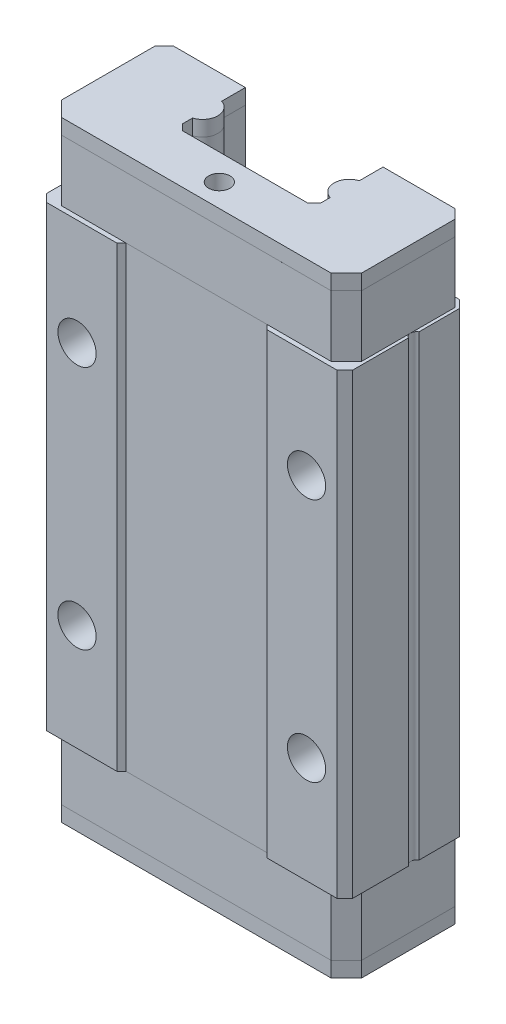
SolidWorks part; units mm, degrees
material "1.4301 (X5CrNi18-10)"
ref_plane "Horní rovina" through (0, 0, 0) normal (0, 0, 1) x (1, 0, 0)
ref_plane "Přední rovina" through (0, 0, 0) normal (0, 1, 0) x (1, 0, 0)
ref_plane "Pravá rovina" through (0, 0, 0) normal (1, 0, 0) x (0, 0, -1)
sketch "Skica1" plane through (0, 0, 0) normal (0, 0, 1) x (1, 0, 0)
  line L1 (-10, 14.95) -> (10, 14.95)
  line L2 (-10, 14.95) -> (-10, -14.95)
  line L3 (-10, -14.95) -> (10, -14.95)
  line L4 (10, 14.95) -> (10, -14.95)
  line L5 (-10, 14.95) -> (10, -14.95) construction
  line L6 (-10, -14.95) -> (10, 14.95) construction
  point P0 (0, 0)
  dimension "D1" = 20
  dimension "D2" = 29.9
extrude "Přidat vysunutím1" add sketch "Skica1" along normal blind 8
chamfer "Zkosení1" distance 0.5 angle 45 4 edges at (-10, 0, 0) (-10, 0, 8) (10, 0, 0) (10, 0, 8)
sketch "Skica2" plane through (0, -14.95, 0) normal (0, -1, 0) x (1, 0, 0)
  line L0 (0, 0) -> (0, 14.7686) construction
  line L1 (-9.5, 0) -> (9.5, 0) construction
  line L2 (-9.5, 8) -> (9.5, 8) construction
  line L4 (-4.9, 8) -> (4.9, 8)
  line L5 (-4.6, 7.7) -> (4.6, 7.7)
  line L6 (-4.9, 8) -> (-4.6, 7.7)
  line L7 (4.6, 7.7) -> (4.9, 8)
  point P9 (0.0002, 10)
  point P12 (0, 8)
  point P15 (0, 7.7)
  dimension "D1" = 9.2
  dimension "D2" = 9.8
  dimension "D3" = 0.3
extrude "Odebrat vysunutím1" cut sketch "Skica2" against normal through all
hole_wizard "M3 závit1" positions "Skica3" profile "Skica4" tap size "M3" standard "ISO"
sketch "Skica3" plane through (0, 0, 8) normal (0, 0, 1) x (1, 0, 0)
  line L1 (-8.5493, 0) -> (8.6735, 0) construction
  line L3 (0, 11.7876) -> (0, -10.7203) construction
  point P0 (-7.5, 8)
  point P2 (-7.5, -8)
  point P4 (7.5, -8)
  point P6 (7.5, 8)
  dimension "D1" = 8
  dimension "D2" = 7.5
  dimension "D3" = 8
  dimension "D4" = 7.5
  dimension "D5" = 7.5
  dimension "D6" = 8
  dimension "D7" = 8
  dimension "D8" = 7.5
sketch "Skica4" plane through (-7.5, 8, 8) normal (1, 0, 0) x (0, -1, 0)
  line L0 (0, 0) -> (0, 6.7511)
  line L1 (0, 6.7511) -> (1.25, 6)
  line L2 (1.25, 6) -> (1.25, 0)
  line L5 (1.25, 0) -> (0, 0)
  line L10 (0, 6.7511) -> (-1.25, 6) construction
  line L11 (0, -6.35) -> (0, 107.95) construction
  dimension "Průměr závitníku" = 2.5
  dimension "Hloubka závitníku" = 6
  dimension "Úhel vrtání" = 118
sketch "Skica5" plane through (0, -14.95, 0) normal (0, -1, 0) x (1, 0, 0)
  line L0 (-4.6, 7.7) -> (4.6, 7.7) construction
  line L1 (-4.6, 7.7) -> (4.6, 7.7)
  line L2 (0, -1.4037) -> (0, 13.1614) construction
  line L3 (4.6, 7.7) -> (8.8, 7.7)
  line L4 (9.8, 6.7) -> (9.8, 0.6)
  line L5 (10, 7.5) -> (10, 0.5) construction
  line L6 (8.8, 7.7) -> (9.8, 6.7)
  line L7 (9.8, 0.6) -> (9.2, 0)
  line L8 (-9.5, 0) -> (9.5, 0) construction
  line L9 (-9.2, 0) -> (9.2, 0)
  line L10 (-9.8, 0.6) -> (-9.2, 0)
  line L11 (-9.8, 6.7) -> (-9.8, 0.6)
  line L12 (-8.8, 7.7) -> (-9.8, 6.7)
  line L13 (-4.6, 7.7) -> (-8.8, 7.7)
  dimension "D1" = 0.2
  dimension "D2" = 1
  dimension "D3" = 1
  dimension "D4" = 45
  dimension "D5" = 0.6
extrude "Přidat vysunutím2" add sketch "Skica5" along normal blind 4 separate body
sketch "Skica6" plane through (0, -18.95, 0) normal (0, -1, 0) x (1, 0, 0)
  line L8 (8.8, 7.7) -> (-8.8, 7.7)
  line L9 (-8.8, 7.7) -> (-9.8, 6.7)
  line L10 (-9.8, 6.7) -> (-9.8, 0.6)
  line L11 (-9.8, 0.6) -> (-9.2, 0)
  line L12 (-9.2, 0) -> (9.2, 0)
  line L13 (9.2, 0) -> (9.8, 0.6)
  line L14 (9.8, 0.6) -> (9.8, 6.7)
  line L15 (9.8, 6.7) -> (8.8, 7.7)
  line L16 (8.8, 7.7) -> (-8.8, 7.7)
  line L17 (-8.8, 7.7) -> (-9.8, 6.7)
  line L18 (-9.8, 6.7) -> (-9.8, 0.6)
  line L19 (-9.8, 0.6) -> (-9.2, 0)
  line L20 (-9.2, 0) -> (9.2, 0)
  line L21 (9.2, 0) -> (9.8, 0.6)
  line L22 (9.8, 0.6) -> (9.8, 6.7)
  line L23 (9.8, 6.7) -> (8.8, 7.7)
  dimension "D1" = 0
extrude "Přidat vysunutím3" add sketch "Skica6" along normal blind 1
pattern_linear "LinPole1" count 2 spacing 33.9 along (0, 1, 0) of "Přidat vysunutím2"
pattern_linear "LinPole2" count 2 spacing 38.9 along (0, 1, 0) of "Přidat vysunutím3"
sketch "Skica7" plane through (0, -19.95, 0) normal (0, -1, 0) x (1, 0, 0)
  line L0 (-4.5, 1.5461) -> (-4.5, 0)
  line L1 (-4.5, 4.1) -> (-4.5, 3.4539)
  line L2 (-4.1, 4.5) -> (-4.5, 4.1)
  line L3 (-4.1, 4.5) -> (4.1, 4.5)
  line L4 (4.1, 4.5) -> (4.5, 4.1)
  line L5 (4.5, 4.1) -> (4.5, 3.4539)
  line L6 (4.5, 1.5461) -> (4.5, 0)
  line L7 (0, -0.8402) -> (0, 11.4147) construction
  line L8 (-9.2, 0) -> (9.2, 0) construction
  line L9 (-9.2, 0) -> (9.2, 0) construction
  line L10 (-4.5, 0) -> (4.5, 0)
  arc A0 (-4.5, 3.4539) -> (-4.5, 1.5461) centre (-4.8, 2.5) cw
  arc A2 (4.5, 3.4539) -> (4.5, 1.5461) centre (4.8, 2.5) ccw
  point P21 (0, 4.5)
  dimension "D5" = 1
  dimension "D1" = 4.5
  dimension "D2" = 4.5
  dimension "D3" = 0.4
  dimension "D4" = 0.4
  dimension "D6" = 2.5
  dimension "D7" = 0.3
extrude "Odebrat vysunutím2" cut sketch "Skica7" against normal through all
sketch "Skica8" plane through (0, -14.95, 0) normal (0, -1, 0) x (1, 0, 0)
  line L0 (10, 7.5) -> (10, 0.5) construction
  line L1 (4.5, 0) -> (9.5, 0) construction
  line L2 (10, 3.8464) -> (10, 3.1536)
  arc A0 (10, 3.1536) -> (10, 3.8464) centre (10.2, 3.5) cw
  dimension "D1" = 0.4
  dimension "D2" = 0.2
  dimension "D3" = 3.5
extrude "Odebrat vysunutím3" cut sketch "Skica8" against normal through all
sketch "Skica9" plane through (0, 19.95, 0) normal (0, 1, 0) x (1, 0, 0)
  line L0 (0, 0) -> (0, -11.8309) construction
  line L2 (9.5, -8) -> (4.9, -8) construction
  circle A0 centre (0, -6.2) radius 0.7
  dimension "D1" = 1.4
  dimension "D2" = 1.8
extrude "Odebrat vysunutím4" cut sketch "Skica9" against normal blind 2
mirror "Zrcadlit4" about plane through (0, 0, 0) normal (0, 1, 0) of "Odebrat vysunutím4"
equation "\"D3@Skica3\" = \"D1@Skica3\""
equation "\"D4@Skica3\"=\"D2@Skica3\""
equation "\"D5@Skica3\"=\"D2@Skica3\""
equation "\"D6@Skica3\" = \"D1@Skica3\""
equation "\"D7@Skica3\" = \"D1@Skica3\""
equation "\"D8@Skica3\"=\"D2@Skica3\""
equation "\"D3@Skica5\"=\"D2@Skica5\""
equation "\"D3@LinPole1\"= \"D2@Skica1\" + \"D1@Přidat vysunutím2\""
equation "\"D3@LinPole2\"= \"D2@Skica1\" + 2 * \"D1@Přidat vysunutím2\" + \"D1@Přidat vysunutím3\""
equation "\"D4@Skica7\"=\"D3@Skica7\""
